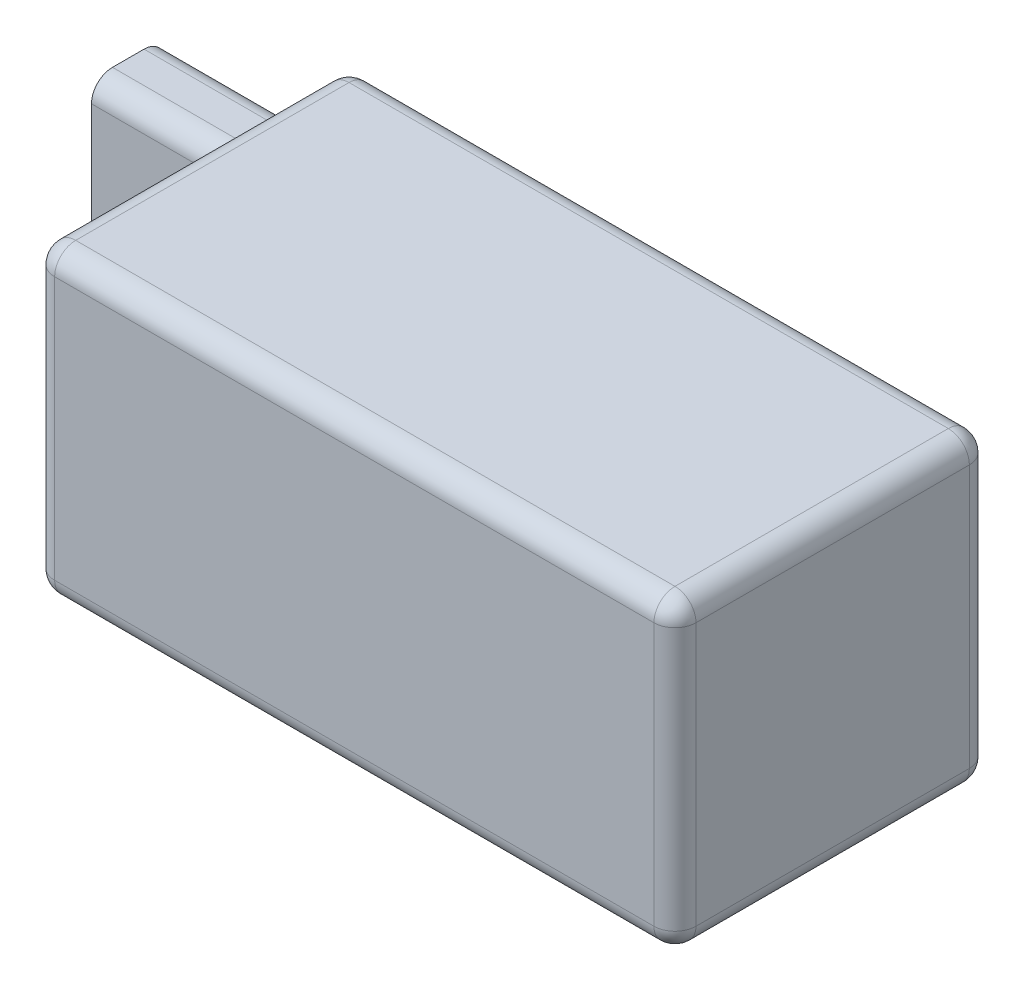
SolidWorks part; units mm, degrees
ref_plane "Front Plane" through (0, 0, 0) normal (0, 0, 1) x (1, 0, 0)
ref_plane "Top Plane" through (0, 0, 0) normal (0, 1, 0) x (1, 0, 0)
ref_plane "Right Plane" through (0, 0, 0) normal (1, 0, 0) x (0, 0, -1)
sketch "Sketch1" plane through (0, 0, 0) normal (0, 1, 0) x (1, 0, 0)
  line L1 (30.5, -15) -> (-30.5, -15)
  line L2 (30.5, -15) -> (30.5, 15)
  line L3 (30.5, 15) -> (-30.5, 15)
  line L4 (-30.5, -15) -> (-30.5, 15)
  line L5 (30.5, -15) -> (-30.5, 15) construction
  line L6 (30.5, 15) -> (-30.5, -15) construction
  point P0 (0, 0)
  dimension "D1" = 30
  dimension "D2" = 61
extrude "Boss-Extrude1" add sketch "Sketch1" along normal blind 29
sketch "Sketch2" plane through (-30.5, 0, 0) normal (-1, 0, 0) x (0, 0, 1)
  line L0 (-11.5, 29) -> (-11.5, 0) construction
  line L1 (-8, 7) -> (-15, 7)
  line L2 (-8, 7) -> (-8, 22)
  line L3 (-8, 22) -> (-15, 22)
  line L4 (-15, 7) -> (-15, 22)
  line L5 (-8, 7) -> (-15, 22) construction
  line L6 (-8, 22) -> (-15, 7) construction
  line L7 (-15, 29) -> (15, 29) construction
  line L8 (-15, 0) -> (15, 0) construction
  line L9 (-15, 29) -> (-15, 0) construction
  point P0 (-11.5, 14.5)
  dimension "D1" = 15
  dimension "D2" = 7
extrude "Boss-Extrude2" add sketch "Sketch2" along normal blind 17.5
fillet "Fillet1" radius 2 4 edges at (-39.25, 7, -15) (-39.25, 7, -8) (-39.25, 22, -15) (-39.25, 22, -8)
fillet "Fillet2" radius 2 13 edges at (30.5, 14.5, -15) (0, 29, -15) (30.5, 29, 0) (-30.5, 29, 0) (30.5, 0, 0) (0, 0, -15) (-30.5, 0, 0) (-30.5, 14.5, 15) (0, 29, 15) (30.5, 14.5, 15) (0, 0, 15) (-30.5, 24.5, -15) (-30.5, 4.5, -15)
